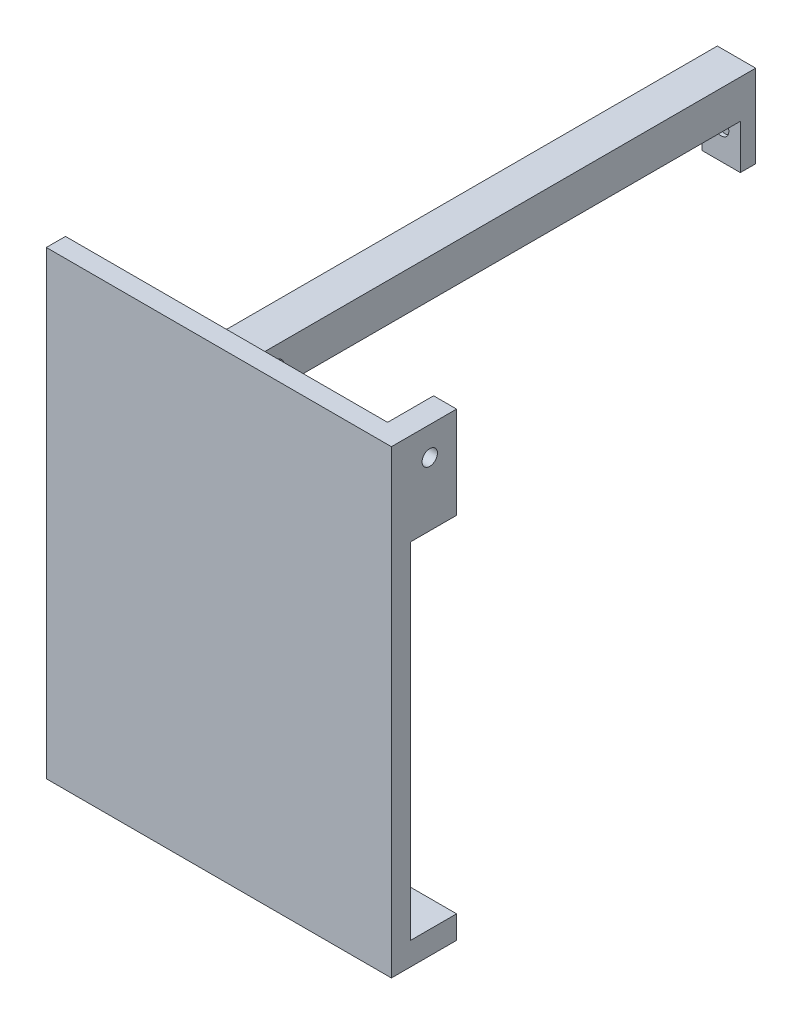
SolidWorks part; units mm, degrees
ref_plane "Front Plane" through (0, 0, 0) normal (0, 0, 1) x (1, 0, 0)
ref_plane "Top Plane" through (0, 0, 0) normal (0, 1, 0) x (1, 0, 0)
ref_plane "Right Plane" through (0, 0, 0) normal (1, 0, 0) x (0, 0, -1)
sketch "Sketch1" plane through (0, 0, 0) normal (0, 0, 1) x (1, 0, 0)
  line L1 (-35.2151, 27.1505) -> (14.7849, 27.1505)
  line L2 (-35.2151, 27.1505) -> (-35.2151, -22.8495)
  line L3 (-35.2151, -22.8495) -> (14.7849, -22.8495)
  line L4 (14.7849, 27.1505) -> (14.7849, -22.8495)
  dimension "D1" = 50
  dimension "D2" = 50
extrude "Boss-Extrude1" add sketch "Sketch1" along normal blind 650
sketch "Sketch2" plane through (0, 0, 650) normal (0, 0, 1) x (1, 0, 0)
  line L0 (-35.2151, -22.8495) -> (14.7849, -22.8495) construction
  line L5 (-235.2151, 37.1505) -> (214.7849, 37.1505)
  line L6 (-235.2151, 37.1505) -> (-235.2151, -562.8495)
  line L7 (-235.2151, -562.8495) -> (214.7849, -562.8495)
  line L8 (214.7849, 37.1505) -> (214.7849, -562.8495)
  line L9 (14.7849, 27.1505) -> (-35.2151, 27.1505) construction
  point P3 (-10.2151, -22.8495)
  point P7 (-10.2151, -562.8495)
  point P10 (-10.2151, 27.1505)
  point P11 (-10.2151, 37.1505)
  dimension "D1" = 450
  dimension "D2" = 10
  dimension "D3" = 600
extrude "Boss-Extrude2" add sketch "Sketch2" along normal blind 25
sketch "Sketch4" plane through (0, 0, 650) normal (0, 0, -1) x (-1, 0, 0)
  line L0 (235.2151, 37.1505) -> (235.2151, -562.8495) construction
  line L1 (-214.7849, -562.8495) -> (235.2151, -562.8495)
  line L2 (-214.7849, -562.8495) -> (-214.7849, -532.8495)
  line L3 (-214.7849, -532.8495) -> (235.2151, -532.8495)
  line L4 (235.2151, -562.8495) -> (235.2151, -532.8495)
  line L5 (-214.7849, -562.8495) -> (-214.7849, 37.1505) construction
  line L6 (-214.7849, -52.8495) -> (235.2151, -52.8495)
  line L7 (-214.7849, -52.8495) -> (-214.7849, -82.8495)
  line L8 (-214.7849, -82.8495) -> (235.2151, -82.8495)
  line L9 (235.2151, -52.8495) -> (235.2151, -82.8495)
  line L10 (35.2151, -22.8495) -> (-14.7849, -22.8495) construction
  dimension "D1" = 30
  dimension "D2" = 30
extrude "Boss-Extrude3" add sketch "Sketch4" along normal blind 60
sketch "Sketch5" plane through (0, -562.8495, 0) normal (0, -1, 0) x (1, 0, 0)
  line L0 (214.7849, 590) -> (-235.2151, 590) construction
  circle A0 centre (-10.2151, 625) radius 10
  point P5 (-10.2151, 590)
  dimension "D2" = 20
  dimension "D1" = 35
extrude "Cut-Extrude1" cut sketch "Sketch5" against normal up to surface (510 mm away) up to face at (-10.2151, -52.8495, 620)
sketch "Sketch7" plane through (0, -22.8495, 0) normal (0, -1, 0) x (1, 0, 0)
  line L0 (14.7849, 650) -> (14.7849, 0) construction
  line L1 (-35.2151, 0) -> (14.7849, 0)
  line L2 (-35.2151, 0) -> (-35.2151, 20)
  line L3 (-35.2151, 20) -> (14.7849, 20)
  line L4 (14.7849, 0) -> (14.7849, 20)
  dimension "D1" = 20
extrude "Boss-Extrude4" add sketch "Sketch7" along normal blind 58
sketch "Sketch8" plane through (0, 0, 650) normal (0, 0, -1) x (-1, 0, 0)
  line L0 (-14.7849, -22.8495) -> (35.2151, -22.8495) construction
  circle A0 centre (10.2151, -41.8495) radius 10
  point P6 (10.2151, -22.8495)
  dimension "D1" = 20
  dimension "D2" = 19
extrude "Cut-Extrude3" cut sketch "Sketch8" against normal blind 20 and the other way blind 635
sketch "Sketch9" plane through (0, 0, 650) normal (0, 0, -1) x (-1, 0, 0)
  line L0 (-214.7849, 37.1505) -> (235.2151, 37.1505) construction
  line L1 (-214.7849, -52.8495) -> (-184.7849, -52.8495)
  line L2 (-214.7849, -52.8495) -> (-214.7849, 37.1505)
  line L3 (-214.7849, 37.1505) -> (-184.7849, 37.1505)
  line L4 (-184.7849, -52.8495) -> (-184.7849, 37.1505)
  dimension "D1" = 30
extrude "Boss-Extrude5" add sketch "Sketch9" along normal up to surface (60 mm away) up to face at (-10.2151, -67.8495, 590)
sketch "Sketch10" plane through (214.7849, 0, 0) normal (1, 0, 0) x (0, 0, -1)
  line L0 (-590, 37.1505) -> (-590, -82.8495) construction
  circle A0 centre (-625, 0) radius 10
  dimension "D1" = 20
  dimension "D2" = 35
extrude "Cut-Extrude4" cut sketch "Sketch10" against normal blind 214
